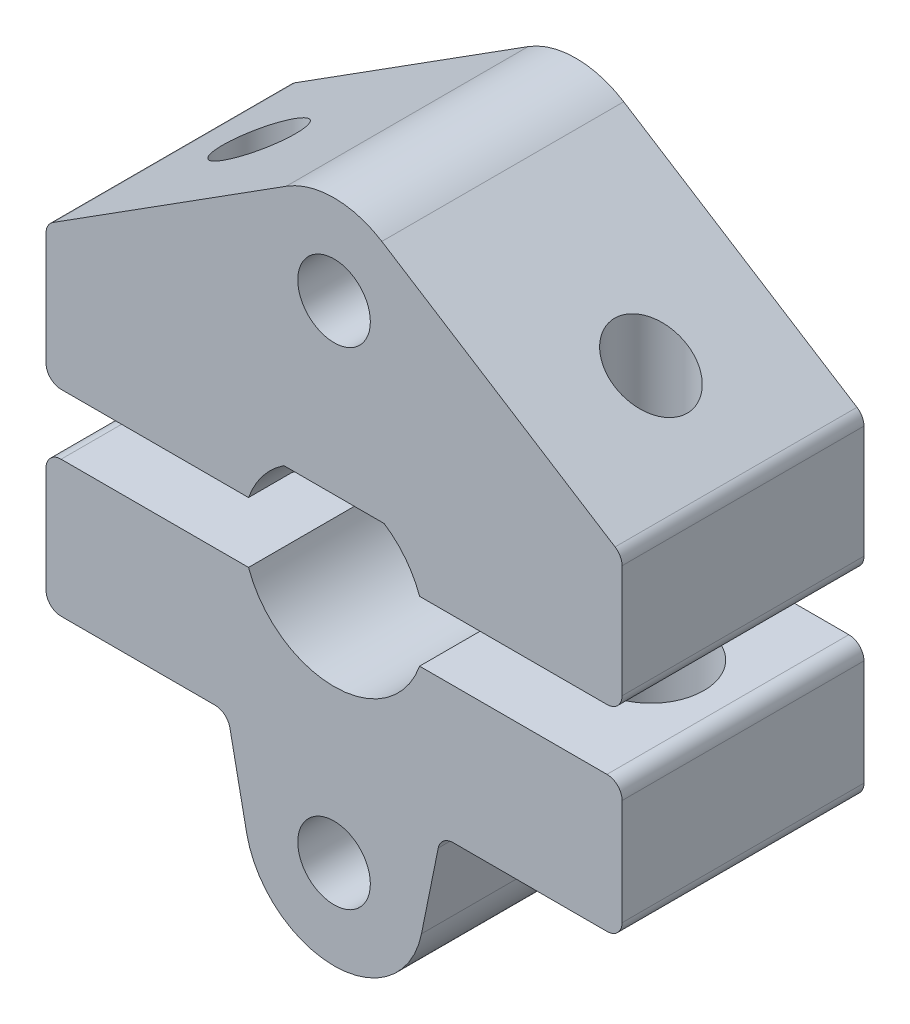
SolidWorks part; units mm, degrees
material "6061-T6 (SS)"
ref_plane "前视基准面" through (0, 0, 0) normal (0, 0, 1) x (1, 0, 0)
ref_plane "上视基准面" through (0, 0, 0) normal (0, 1, 0) x (1, 0, 0)
ref_plane "右视基准面" through (0, 0, 0) normal (1, 0, 0) x (0, 0, -1)
sketch "草图1" plane through (0, 0, 0) normal (0, 0, 1) x (1, 0, 0)
  line L0 (-1.6583, 2.5) -> (1.6583, 2.5)
  line L1 (-9.2941, 5.6473) -> (-1.5803, 10.541)
  line L2 (1.5803, 10.541) -> (9.2941, 5.6473)
  line L3 (-9.5263, 5.2251) -> (-9.5263, 1.5)
  line L4 (-9.0263, 1) -> (-2.8284, 1)
  line L5 (9.5263, 1.5) -> (9.5263, 5.2251)
  line L6 (0, 1) -> (0, 0) construction
  line L7 (-9.0263, -1) -> (-2.8284, -1)
  line L8 (9.5263, -1.5) -> (9.5263, -5)
  line L9 (9.0263, -5.5) -> (3.9352, -5.5)
  line L10 (3.4451, -5.9008) -> (2.8913, -8.6355)
  line L11 (-2.8913, -8.6355) -> (-3.4451, -5.9008)
  line L12 (-3.9352, -5.5) -> (-9.0263, -5.5)
  line L13 (-9.5263, -5) -> (-9.5263, -1.5)
  line L14 (0, 0) -> (0, -1) construction
  line L15 (2.8284, 1) -> (9.0263, 1)
  line L16 (2.8284, -1) -> (9.0263, -1)
  line L17 (9.2941, 5.6473) -> (9.5263, 5.5) construction
  line L18 (9.5263, 5.5) -> (9.5263, 5.2251) construction
  arc A0 (-1.6583, 2.5) -> (-2.8284, 1) centre (0, 0) ccw
  circle A1 centre (0, 0) radius 8.05 construction
  circle A2 centre (0, 8.05) radius 1.2
  circle A3 centre (0, -8.05) radius 1.2
  arc A4 (-1.5803, 10.541) -> (1.5803, 10.541) centre (0, 8.05) cw
  circle A5 centre (0, 0) radius 11 construction
  arc A6 (2.8913, -8.6355) -> (-2.8913, -8.6355) centre (0, -8.05) cw
  arc A7 (-9.5263, 1.5) -> (-9.0263, 1) centre (-9.0263, 1.5) ccw
  arc A8 (-9.2941, 5.6473) -> (-9.5263, 5.2251) centre (-9.0263, 5.2251) ccw
  arc A9 (9.2941, 5.6473) -> (9.5263, 5.2251) centre (9.0263, 5.2251) cw
  arc A10 (9.0263, 1) -> (9.5263, 1.5) centre (9.0263, 1.5) ccw
  arc A11 (-9.0263, -5.5) -> (-9.5263, -5) centre (-9.0263, -5) cw
  arc A12 (-9.0263, -1) -> (-9.5263, -1.5) centre (-9.0263, -1.5) ccw
  arc A13 (9.5263, -5) -> (9.0263, -5.5) centre (9.0263, -5) cw
  arc A14 (9.0263, -1) -> (9.5263, -1.5) centre (9.0263, -1.5) cw
  arc A15 (3.9352, -5.5) -> (3.4451, -5.9008) centre (3.9352, -6) ccw
  arc A16 (-3.4451, -5.9008) -> (-3.9352, -5.5) centre (-3.9352, -6) ccw
  arc A17 (-2.8284, -1) -> (2.8284, -1) centre (0, 0) ccw
  arc A18 (2.8284, 1) -> (1.6583, 2.5) centre (0, 0) ccw
  point P31 (-9.5263, 1)
  point P34 (-9.5263, 5.5)
  point P39 (9.5263, 1)
  point P42 (-9.5263, -5.5)
  point P47 (9.5263, -5.5)
  point P52 (3.5263, -5.5)
  dimension "D1" = 16.1
  dimension "D2" = 6
  dimension "D4" = 2.4
  dimension "D6" = 22
  dimension "D10" = 0.5
  dimension "D5" = 4.5
  dimension "D3" = 2.5
  dimension "D7" = 1
  dimension "D9" = 6
extrude "凸台-拉伸1" add sketch "草图1" along normal blind 8
cosmetic thread "装饰螺纹线3" parameters "D2"=3
cosmetic thread "装饰螺纹线4" parameters "D2"=3
sketch "草图2" plane through (0, -5.5, 0) normal (0, -1, 0) x (1, 0, 0)
  line L0 (-9.5263, 4) -> (-6.4807, 4) construction
  line L1 (-9.5263, 8) -> (-9.5263, 0) construction
  line L2 (-6.4807, 4) -> (6.4807, 4) construction
  line L3 (6.4807, 4) -> (9.5263, 4) construction
  line L4 (9.5263, 8) -> (9.5263, 0) construction
  line L5 (6.4807, 8) -> (6.4807, 4) construction
  line L6 (3.9352, 8) -> (9.0263, 8) construction
  circle A0 centre (6.4807, 4) radius 1.2
  circle A1 centre (-6.4807, 4) radius 1.2
  dimension "D1" = 2.4
extrude "切除-拉伸1" cut sketch "草图2" against normal through all
cosmetic thread "装饰螺纹线1" parameters "D2"=3
cosmetic thread "装饰螺纹线2" parameters "D2"=3
sketch "草图3" plane through (0, -5.5, 0) normal (0, -1, 0) x (1, 0, 0)
  circle A0 centre (-6.4807, 4) radius 1.75
  circle A1 centre (6.4807, 4) radius 1.75
  dimension "D1" = 3.5
extrude "切除-拉伸2" cut sketch "草图3" against normal up to surface (4.5 mm away) up to face at (-5.2807, -1, 4)
